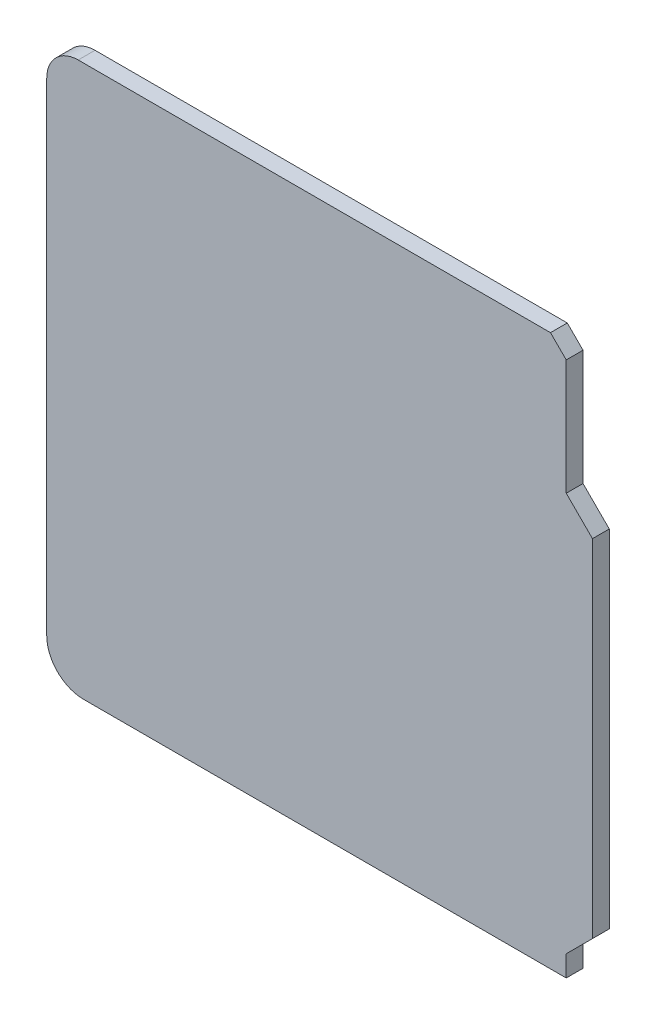
SolidWorks part; units mm, degrees
ref_plane "Plan de face" through (0, 0, 0) normal (0, 0, 1) x (1, 0, 0)
ref_plane "Plan de dessus" through (0, 0, 0) normal (0, 1, 0) x (1, 0, 0)
ref_plane "Plan de droite" through (0, 0, 0) normal (1, 0, 0) x (0, 0, -1)
sketch "Esquisse2" plane through (0, 0, 0) normal (0, 0, 1) x (1, 0, 0)
  line L0 (11.2731, 340.803) -> (790.6064, 340.803) construction
  line L1 (94.6702, 353.6046) -> (584.0036, 353.6046) construction
  line L2 (-24.7093, 32.8902) -> (20.2907, 32.8902)
  line L3 (20.2907, 32.8902) -> (21.7907, 31.3902)
  line L4 (21.7907, 31.3902) -> (21.7907, 20.3902)
  line L5 (21.7907, 20.3902) -> (24.2907, 17.8902)
  line L6 (24.2907, 17.8902) -> (24.2907, -15.1143)
  line L7 (24.2907, -15.1143) -> (21.7907, -17.6143)
  line L8 (21.7907, -17.6143) -> (21.7907, -19.6143)
  line L9 (21.7907, -19.6143) -> (-24.2093, -19.6143)
  line L10 (-27.7093, 29.8902) -> (-27.7093, -16.1143)
  arc A0 (-24.7093, 32.8902) -> (-27.7093, 29.8902) centre (-24.7093, 29.8902) ccw
  arc A1 (-27.7093, -16.1143) -> (-24.2093, -19.6143) centre (-24.2093, -16.1143) ccw
extrude "Boss.-Extru.2" add sketch "Esquisse2" along normal blind 1.6 separate body
